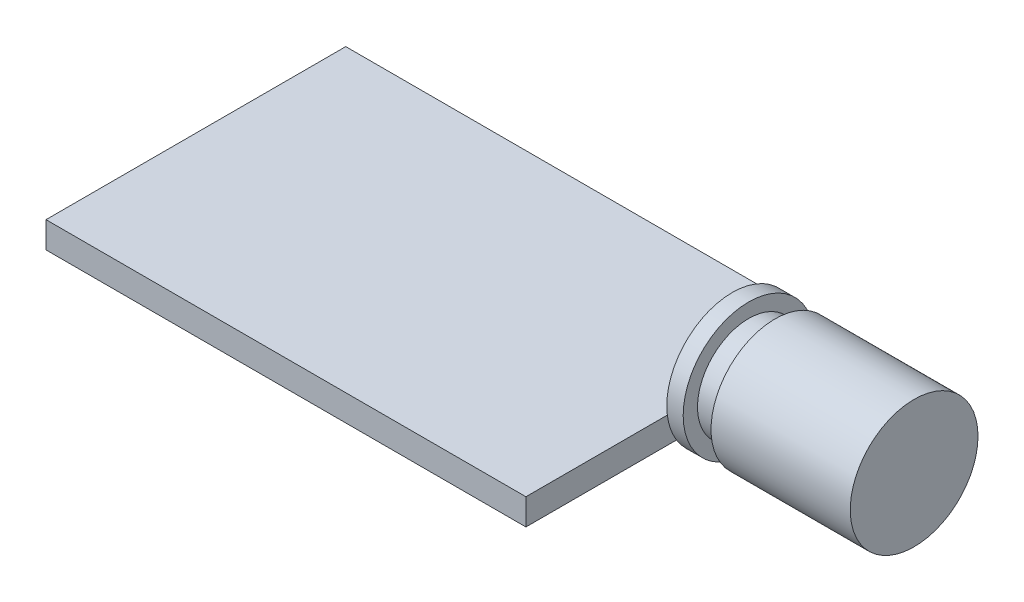
SolidWorks part; units mm, degrees
ref_plane "Front Plane" through (0, 0, 0) normal (0, 0, 1) x (1, 0, 0)
ref_plane "Top Plane" through (0, 0, 0) normal (0, 1, 0) x (1, 0, 0)
ref_plane "Right Plane" through (0, 0, 0) normal (1, 0, 0) x (0, 0, -1)
sketch "Sketch2" plane through (0, 0, 0) normal (0, 1, 0) x (1, 0, 0)
  line L1 (0, 0) -> (29.3, 0)
  line L2 (0, 0) -> (0, 18.3)
  line L3 (0, 18.3) -> (29.3, 18.3)
  line L4 (29.3, 0) -> (29.3, 18.3)
  dimension "D1" = 29.3
  dimension "D2" = 18.3
extrude "Boss-Extrude1" add sketch "Sketch2" along normal blind 1.6
sketch "Sketch3" plane through (29.3, 0, 0) normal (1, 0, 0) x (0, 0, -1)
  line L1 (18.3, 1.6) -> (18.3, 0) construction
  line L2 (0, 1.6) -> (18.3, 1.6) construction
  circle A0 centre (12.6, 2.1) radius 4
  dimension "D2" = 8
  dimension "D3" = 5.7
  dimension "D1" = 0.5
extrude "Boss-Extrude2" add sketch "Sketch3" along normal blind 1
sketch "Sketch4" plane through (30.3, 0, 0) normal (1, 0, 0) x (0, 0, -1)
  circle A0 centre (12.6, 2.1) radius 3.125
  circle A1 centre (12.6, 2.1) radius 4 construction
  dimension "D1" = 6.25
extrude "Boss-Extrude3" add sketch "Sketch4" along normal blind 1.6
sketch "Sketch5" plane through (31.9, 0, 0) normal (1, 0, 0) x (0, 0, -1)
  circle A0 centre (12.6, 2.1) radius 3.9
  circle A1 centre (12.6, 2.1) radius 3.125 construction
  dimension "D1" = 7.8
extrude "Boss-Extrude4" add sketch "Sketch5" along normal blind 8.5
